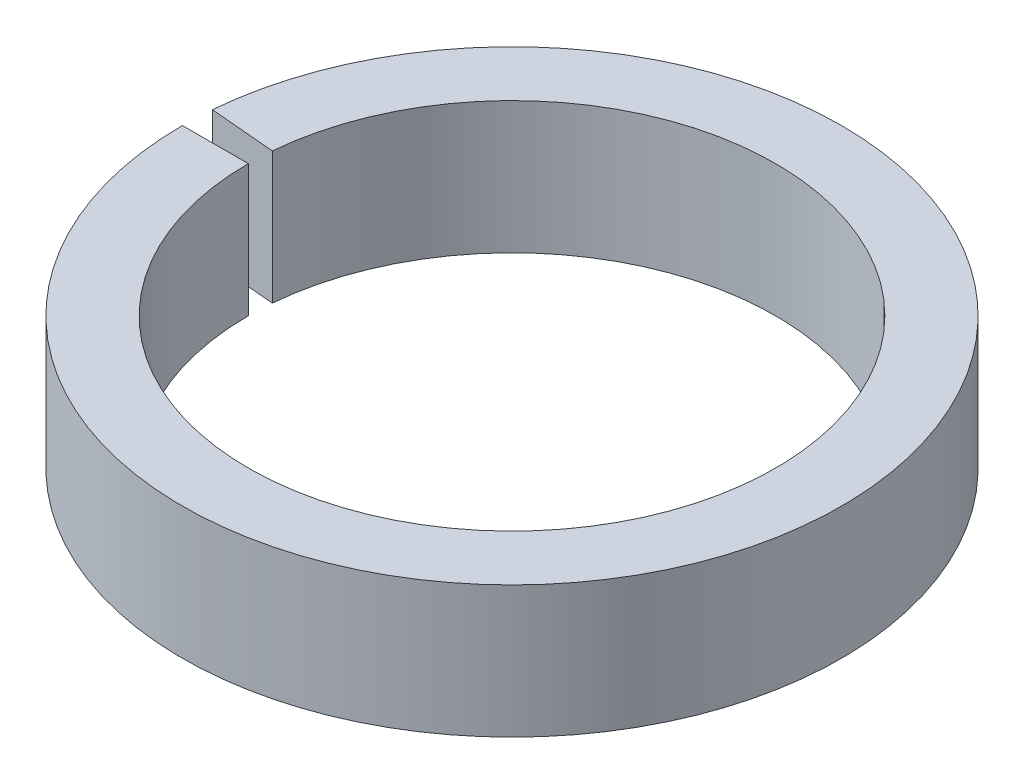
SolidWorks part; units mm, degrees
material "Zoltek Panex 33"
ref_plane "Front Plane" through (0, 0, 0) normal (0, 0, 1) x (1, 0, 0)
ref_plane "Top Plane" through (0, 0, 0) normal (0, 1, 0) x (1, 0, 0)
ref_plane "Right Plane" through (0, 0, 0) normal (1, 0, 0) x (0, 0, -1)
sketch "Sketch1" plane through (0, 0, 0) normal (0, 0, 1) x (1, 0, 0)
  line L0 (0, 0) -> (0, 3.175) construction
  line L2 (-7.9375, 0) -> (-6.35, 0)
  line L3 (-7.9375, 0) -> (-7.9375, 3.175)
  line L4 (-7.9375, 3.175) -> (-6.35, 3.175)
  line L5 (-6.35, 0) -> (-6.35, 3.175)
  dimension "D1" = 3.175
  dimension "D2" = 12.7
  dimension "D3" = 1.5875
revolve "Revolve1" add sketch "Sketch1" angle 355 about L0
